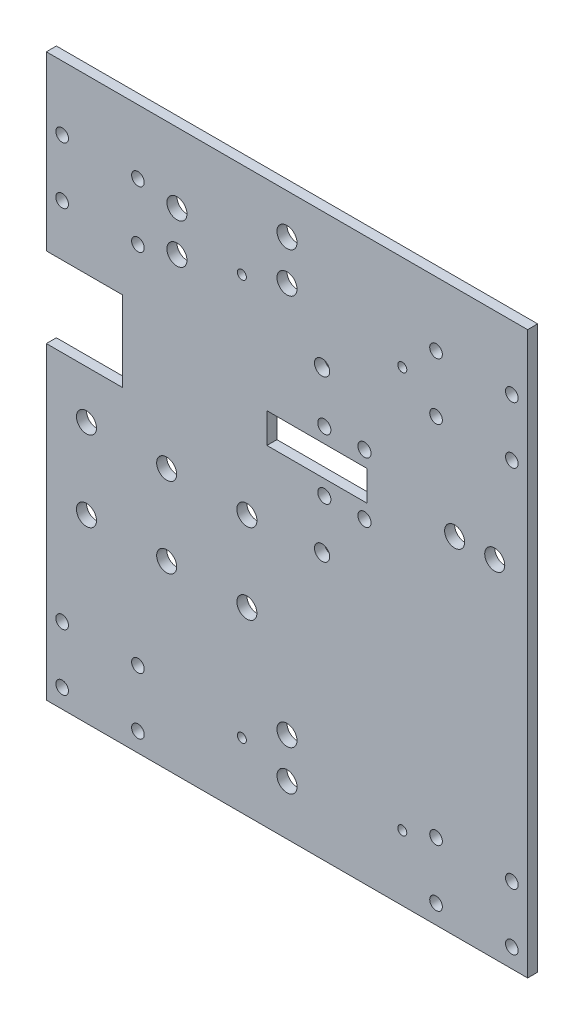
SolidWorks part; units mm, degrees
ref_plane "Front Plane" through (0, 0, 0) normal (0, 0, 1) x (1, 0, 0)
ref_plane "Top Plane" through (0, 0, 0) normal (0, 1, 0) x (1, 0, 0)
ref_plane "Right Plane" through (0, 0, 0) normal (1, 0, 0) x (0, 0, -1)
sketch "Sketch1" plane through (0, 0, 0) normal (0, 0, 1) x (1, 0, 0)
  line L0 (76.2, 177.8) -> (76.2, 0) construction
  line L1 (0, 0) -> (152.4, 0)
  line L2 (0, 0) -> (0, 97.79)
  line L3 (0, 177.8) -> (152.4, 177.8)
  line L4 (152.4, 0) -> (152.4, 177.8)
  line L5 (38.1, 82.55) -> (63.5, 82.55) construction
  line L6 (101.6, 104.775) -> (69.85, 104.775)
  line L7 (101.6, 104.775) -> (101.6, 114.3)
  line L8 (101.6, 114.3) -> (69.85, 114.3)
  line L9 (69.85, 104.775) -> (69.85, 114.3)
  line L10 (38.1, 57.15) -> (63.5, 57.15) construction
  line L11 (50.8, 82.55) -> (50.8, 57.15) construction
  line L12 (101.6, 109.5375) -> (135.289, 109.5375) construction
  line L13 (69.85, 109.5375) -> (101.6, 109.5375) construction
  line L14 (87.3125, 114.3) -> (87.3125, 104.775) construction
  line L15 (0, 97.79) -> (24.1711, 97.79)
  line L16 (24.1711, 97.79) -> (24.1711, 123.19)
  line L17 (24.1711, 123.19) -> (0, 123.19)
  line L18 (0, 123.19) -> (0, 177.8)
  circle A0 centre (38.1, 82.55) radius 3.175
  circle A1 centre (63.5, 82.55) radius 3.175
  circle A2 centre (38.1, 57.15) radius 3.175
  circle A3 centre (63.5, 57.15) radius 3.175
  circle A4 centre (88.0237, 100.0125) radius 2.0828
  circle A5 centre (100.7237, 100.0125) radius 2.0828
  circle A6 centre (88.0237, 119.0625) radius 2.0828
  circle A7 centre (100.7237, 119.0625) radius 2.0828
  circle A8 centre (129.286, 109.5375) radius 3.175
  circle A9 centre (123.4, 139.48) radius 2
  circle A10 centre (147.4, 139.48) radius 2
  circle A11 centre (123.4, 157.48) radius 2
  circle A12 centre (147.4, 157.48) radius 2
  circle A13 centre (5, 6) radius 2
  circle A14 centre (29, 6) radius 2
  circle A15 centre (5, 24) radius 2
  circle A16 centre (29, 24) radius 2
  circle A17 centre (5, 139.48) radius 2
  circle A18 centre (29, 139.48) radius 2
  circle A19 centre (5, 157.48) radius 2
  circle A20 centre (29, 157.48) radius 2
  circle A21 centre (123.4, 6) radius 2
  circle A22 centre (147.4, 6) radius 2
  circle A23 centre (123.4, 24) radius 2
  circle A24 centre (147.4, 24) radius 2
  circle A25 centre (41.35, 155.575) radius 3.175
  circle A26 centre (41.35, 142.875) radius 3.175
  circle A27 centre (12.7, 57.15) radius 3.175
  circle A28 centre (12.7, 82.55) radius 3.175
  circle A29 centre (141.986, 109.5375) radius 3.175
  circle A30 centre (87.3125, 84.1375) radius 2.413
  circle A31 centre (87.3125, 134.9375) radius 2.413
  circle A32 centre (61.9125, 147.6375) radius 1.4224
  circle A33 centre (112.7125, 147.6375) radius 1.4224
  circle A34 centre (112.7125, 20.6375) radius 1.4224
  circle A35 centre (61.9125, 20.6375) radius 1.4224
  circle A36 centre (76.2, 28.575) radius 3.175
  circle A37 centre (76.2, 15.875) radius 3.175
  circle A38 centre (76.2, 165.1) radius 3.175
  circle A39 centre (76.2, 152.4) radius 3.175
  dimension "D4" = 6.35
  dimension "D7" = 57.15
  dimension "D10" = 24
  dimension "D12" = 4
  dimension "D15" = 4
  dimension "D8" = 38.1
  dimension "D9" = 4
  dimension "D18" = 4
  dimension "D25" = 6.35
  dimension "D29" = 6.35
  dimension "D37" = 4.1656
  dimension "D39" = 18.1737
  dimension "D42" = 6.35
  dimension "D43" = 12.7
  dimension "D44" = 27.686
  dimension "D45" = 4.826
  dimension "D49" = 2.8448
  dimension "D54" = 6.35
  dimension "D57" = 15.875
  dimension "D30" = 25.4
  dimension "D32" = 95.25
  dimension "D60" = 15.24
  dimension "D31" = 6.35
  dimension "D1" = 152.4
  dimension "D2" = 177.8
  dimension "D5" = 25.4
  dimension "D6" = 25.4
  dimension "D11" = 18
  dimension "D13" = 24
  dimension "D14" = 18
  dimension "D16" = 24
  dimension "D17" = 18
  dimension "D19" = 24
  dimension "D20" = 18
  dimension "D21" = 5
  dimension "D22" = 5
  dimension "D23" = 6
  dimension "D24" = 20.32
  dimension "D26" = 12.7
  dimension "D27" = 22.225
  dimension "D28" = 12.35
  dimension "D33" = 31.75
  dimension "D34" = 9.525
  dimension "D35" = 19.05
  dimension "D36" = 22.225
  dimension "D38" = 12.7
  dimension "D40" = 4.7625
  dimension "D41" = 4.7625
  dimension "D46" = 50.8
  dimension "D47" = 50.8
  dimension "D48" = 14.2875
  dimension "D50" = 14.2875
  dimension "D51" = 127
  dimension "D52" = 38.1
  dimension "D53" = 50.8
  dimension "D55" = 12.7
  dimension "D56" = 12.7
  dimension "D58" = 12.7
  dimension "D59" = 25.4
  dimension "D61" = 25.4
extrude "Boss-Extrude1" add sketch "Sketch1" along normal blind 3.175
